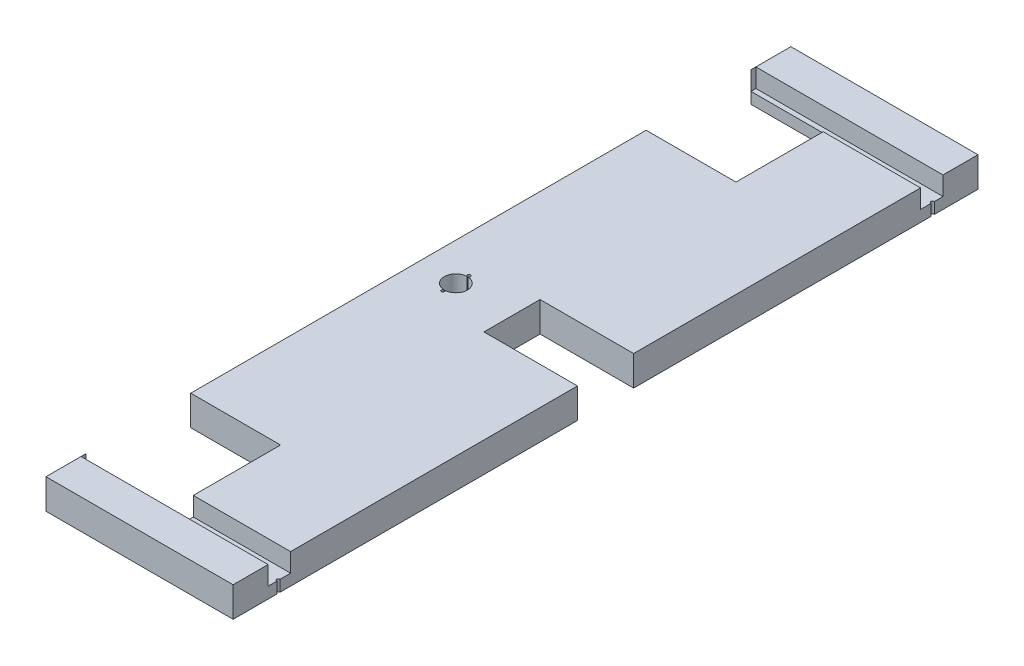
SolidWorks part; units mm, degrees
ref_plane "Front Plane" through (0, 0, 0) normal (0, 0, 1) x (1, 0, 0)
ref_plane "Top Plane" through (0, 0, 0) normal (0, 1, 0) x (1, 0, 0)
ref_plane "Right Plane" through (0, 0, 0) normal (1, 0, 0) x (0, 0, -1)
sketch "Sketch" plane through (0, 0, 0) normal (0, 1, 0) x (1, 0, 0)
  line L1 (0, 191.7809) -> (250, 191.7809)
  line L2 (0, 191.7809) -> (0, 138.4113)
  line L3 (0, -803.3697) -> (250, -803.3697)
  line L4 (250, 191.7809) -> (250, 133.4556)
  line L5 (0, -803.3697) -> (50, -803.3697) construction
  line L6 (50, -803.3697) -> (50, 191.7809) construction
  line L7 (0, -305.7944) -> (250, -305.7944) construction
  line L8 (0, -750) -> (0, -803.3697)
  line L9 (0, -750) -> (120, -750)
  line L11 (0, -610) -> (120, -610)
  line L12 (120, -750) -> (120, -610)
  line L13 (120, 138.4113) -> (120, -1.5887)
  line L14 (0, -1.5887) -> (120, -1.5887)
  line L15 (0, 138.4113) -> (120, 138.4113)
  line L16 (0, -1.5887) -> (0, -610)
  line L17 (250, 128.9556) -> (250, -268.2944)
  line L18 (250, -745.0444) -> (250, -803.3697)
  line L19 (250, -343.2944) -> (250, -740.5444)
  line L20 (250, -268.2944) -> (125, -268.2944)
  line L23 (125, -268.2944) -> (125, -343.2944)
  line L24 (250, -343.2944) -> (125, -343.2944)
  circle A0 centre (50, -305.7944) radius 17.5 construction
  arc A2 (50.5122, -290.2986) -> (49.4878, -290.2986) centre (50, -288.2944) ccw
  arc A3 (49.8778, -321.2981) -> (50.1222, -321.2981) centre (50, -323.2944) ccw
  arc A4 (49.4878, -290.2986) -> (49.8778, -321.2981) centre (50, -305.7944) ccw
  arc A5 (50.1222, -321.2981) -> (50.5122, -290.2986) centre (50, -305.7944) ccw
  circle A6 centre (125, 131.2056) radius 2.25
  circle A7 centre (150, 131.2056) radius 2.25
  circle A8 centre (175, 131.2056) radius 2.25
  circle A9 centre (200, 131.2056) radius 2.25
  circle A10 centre (225, 131.2056) radius 2.25
  arc A11 (250, 133.4556) -> (250, 128.9556) centre (250, 131.2056) ccw
  arc A12 (250, -745.0444) -> (250, -740.5444) centre (250, -742.7944) cw
  circle A13 centre (225, -742.7944) radius 2.25
  circle A14 centre (200, -742.7944) radius 2.25
  circle A15 centre (175, -742.7944) radius 2.25
  circle A16 centre (150, -742.7944) radius 2.25
  circle A17 centre (125, -742.7944) radius 2.25
  point P56 (0, 0)
  point P57 (0, 0)
  point P58 (0, 0)
  point P60 (0, 0)
  dimension "D1" = 6
extrude "Boss-Extrude3" add sketch "Sketch" along normal blind 40
sketch "Sketch1" plane through (0, 40, 0) normal (0, 1, 0) x (1, 0, 0)
  line L0 (250, 191.7809) -> (250, 133.4556) construction
  line L1 (250, 145) -> (0.0503, 145)
  line L2 (250, 145) -> (250, 115)
  line L3 (250, 115) -> (0.0503, 115)
  line L4 (0.0503, 145) -> (0.0503, 115)
  line L6 (0, -305.7944) -> (250, -305.7944) construction
  line L7 (0.0503, -756.5887) -> (0.0503, -726.5887)
  line L8 (250, -726.5887) -> (0.0503, -726.5887)
  line L9 (250, -756.5887) -> (250, -726.5887)
  line L10 (250, -756.5887) -> (0.0503, -756.5887)
  point P14 (0, 0)
  point P15 (0, 0)
extrude "Cut-Extrude1" cut sketch "Sketch1" against normal blind 25
